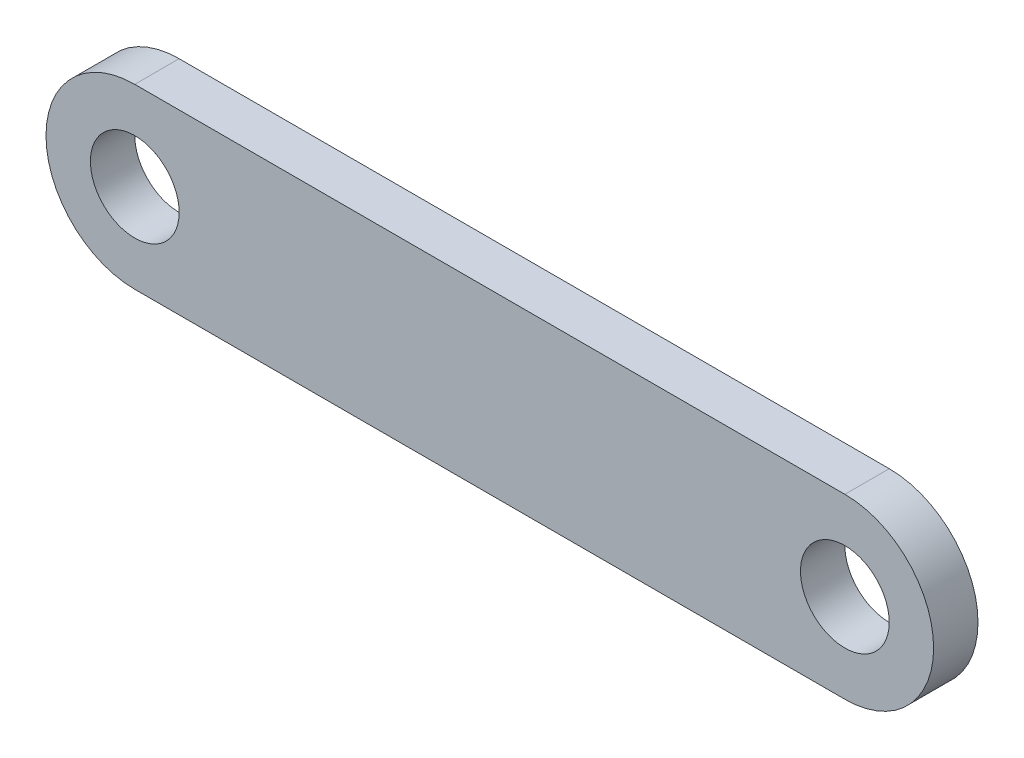
SolidWorks part; units mm, degrees
ref_plane "Front Plane" through (0, 0, 0) normal (0, 0, 1) x (1, 0, 0)
ref_plane "Top Plane" through (0, 0, 0) normal (0, 1, 0) x (1, 0, 0)
ref_plane "Right Plane" through (0, 0, 0) normal (1, 0, 0) x (0, 0, -1)
sketch "Sketch1" plane through (0, 0, 0) normal (0, 0, 1) x (1, 0, 0)
  line L0 (19.1995, -0.5085) -> (-12.8005, -0.5085) construction
  line L1 (19.1995, -4.5085) -> (-12.8005, -4.5085)
  line L2 (19.1995, 3.4915) -> (-12.8005, 3.4915)
  arc A0 (19.1995, -4.5085) -> (19.1995, 3.4915) centre (19.1995, -0.5085) ccw
  arc A1 (-12.8005, 3.4915) -> (-12.8005, -4.5085) centre (-12.8005, -0.5085) ccw
  circle A2 centre (19.1995, -0.5085) radius 2
  circle A3 centre (-12.8005, -0.5085) radius 2
  point P2 (3.1995, -0.5085)
  dimension "D3" = 4
  dimension "D1" = 8
  dimension "D2" = 32
extrude "Boss-Extrude1" add sketch "Sketch1" along normal mid plane 2
